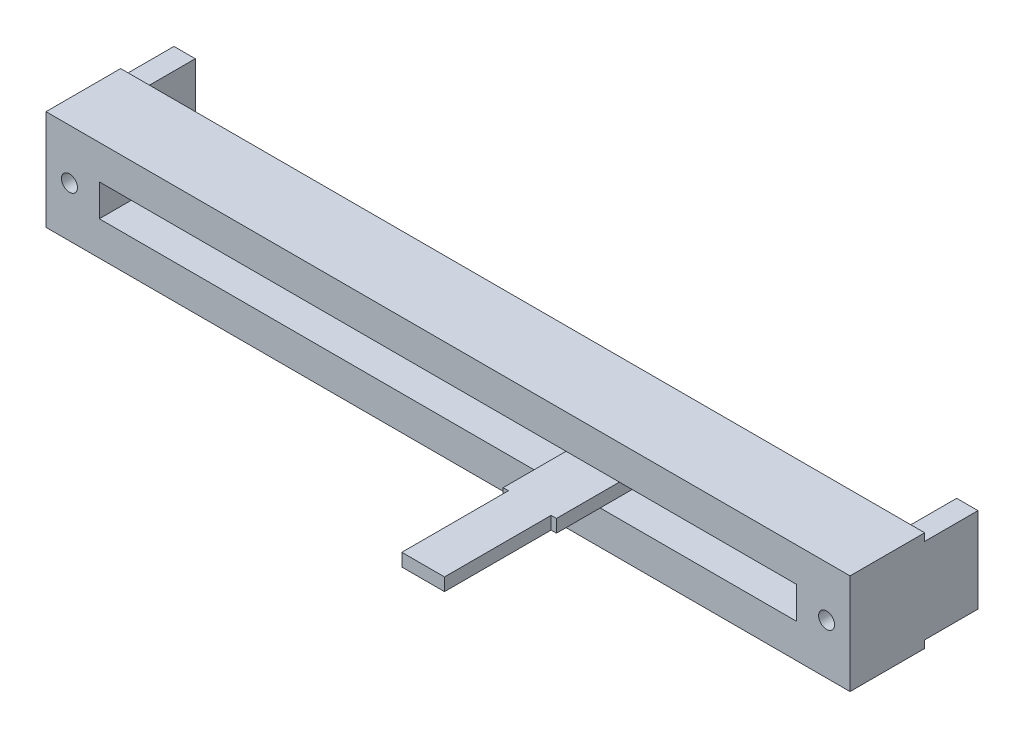
SolidWorks part; units mm, degrees
ref_plane "Спереди" through (0, 0, 0) normal (0, 0, 1) x (1, 0, 0)
ref_plane "Сверху" through (0, 0, 0) normal (0, 1, 0) x (1, 0, 0)
ref_plane "Справа" through (0, 0, 0) normal (1, 0, 0) x (0, 0, -1)
sketch "Sketch1" plane through (0, 0, 0) normal (0, 0, 1) x (1, 0, 0)
  line L0 (-41.71, 0) -> (47.3816, 0) construction
  line L1 (0, 16.1825) -> (0, -14.5459) construction
  line L3 (-37.7, 4.7) -> (37.7, 4.7)
  line L4 (-37.7, 4.7) -> (-37.7, -4.7)
  line L5 (-37.7, -4.7) -> (37.7, -4.7)
  line L6 (37.7, 4.7) -> (37.7, -4.7)
  dimension "D1" = 9.4
  dimension "D2" = 75.4
extrude "Boss-Extrude1" add sketch "Sketch1" along normal blind 7
sketch "Sketch2" plane through (0, 0, 7) normal (0, 0, 1) x (1, 0, 0)
  line L0 (-37.7, 0) -> (37.7, 0) construction
  line L1 (-37.7, 4.7) -> (-37.7, -4.7) construction
  line L2 (37.7, -4.7) -> (37.7, 4.7) construction
  line L3 (0, 4.7) -> (0, -4.7) construction
  line L4 (37.7, 4.7) -> (-37.7, 4.7) construction
  line L5 (-37.7, -4.7) -> (37.7, -4.7) construction
  line L7 (-32.7, 1.5) -> (32.7, 1.5)
  line L8 (-32.7, 1.5) -> (-32.7, -1.5)
  line L9 (-32.7, -1.5) -> (32.7, -1.5)
  line L10 (32.7, 1.5) -> (32.7, -1.5)
  circle A0 centre (-35.5, 0) radius 0.75
  circle A1 centre (35.5, 0) radius 0.75
  dimension "D3" = 71
  dimension "D4" = 1.5
  dimension "D1" = 3
  dimension "D2" = 5
extrude "Cut-Extrude1" cut sketch "Sketch2" against normal blind 5
sketch "Sketch3" plane through (0, 0, 0) normal (0, 0, -1) x (-1, 0, 0)
  line L0 (-37.7, -4.7) -> (-37.7, 4.7) construction
  line L1 (-37.7, 4) -> (-35.7, 4)
  line L2 (-37.7, 4) -> (-37.7, -4)
  line L3 (-37.7, -4) -> (-35.7, -4)
  line L4 (-35.7, 4) -> (-35.7, -4)
  line L5 (37.7, 4.7) -> (37.7, -4.7) construction
  line L6 (37.7, 4) -> (35.7, 4)
  line L7 (37.7, 4) -> (37.7, -4)
  line L8 (37.7, -4) -> (35.7, -4)
  line L9 (35.7, 4) -> (35.7, -4)
  line L10 (-37.7, 0) -> (37.7, 0) construction
  dimension "D1" = 8
  dimension "D2" = 2
  dimension "D3" = 2
extrude "Boss-Extrude2" add sketch "Sketch3" along normal blind 5
sketch "Sketch4" plane through (0, 0, 0) normal (0, 1, 0) x (1, 0, 0)
  line L0 (37.7, 0) -> (-37.7, 0) construction
  line L1 (10.1693, 0) -> (15.1693, 0)
  line L2 (10.1693, 0) -> (10.1693, -12)
  line L3 (10.1693, -12) -> (10.6693, -12)
  line L4 (15.1693, 0) -> (15.1693, -12)
  line L5 (14.6693, -12) -> (15.1693, -12)
  line L6 (12.6693, 0) -> (12.6693, -22.7651) construction
  line L7 (10.6693, -12) -> (10.6693, -22)
  line L8 (10.6693, -22) -> (14.6693, -22)
  line L9 (14.6693, -12) -> (14.6693, -22)
  dimension "D1" = 5
  dimension "D2" = 10
  dimension "D3" = 22
  dimension "D4" = 4
extrude "Boss-Extrude3" add sketch "Sketch4" along normal mid plane 1.2
